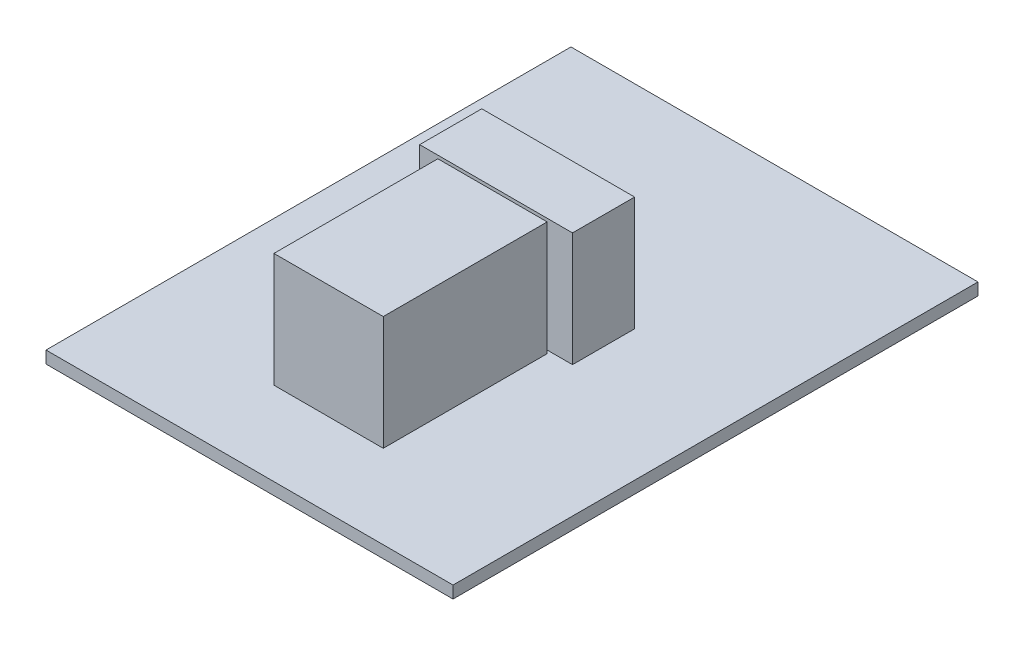
SolidWorks part; units mm, degrees
ref_plane "Front Plane" through (0, 0, 0) normal (0, 0, 1) x (1, 0, 0)
ref_plane "Top Plane" through (0, 0, 0) normal (0, 1, 0) x (1, 0, 0)
ref_plane "Right Plane" through (0, 0, 0) normal (1, 0, 0) x (0, 0, -1)
sketch "Sketch1" plane through (0, 0, 0) normal (0, 1, 0) x (1, 0, 0)
  line L0 (0, 69) -> (0, 0)
  line L1 (0, 0) -> (53.5, 0)
  line L3 (0, 69) -> (53.5, 69)
  line L4 (53.5, 0) -> (53.5, 69)
  dimension "D1" = 53.5
  dimension "D2" = 69
extrude "Boss-Extrude1" add sketch "Sketch1" along normal blind 1.6
sketch "Sketch2" plane through (0, 1.6, 0) normal (0, 1, 0) x (1, 0, 0)
  line L1 (18.9825, 10.9748) -> (33.3533, 10.9748)
  line L2 (18.9825, 10.9748) -> (18.9825, 32.5198)
  line L3 (18.9825, 32.5198) -> (33.3533, 32.5198)
  line L4 (33.3533, 10.9748) -> (33.3533, 32.5198)
  line L5 (16.1779, 32.9338) -> (36.2692, 32.9338)
  line L6 (16.1779, 32.9338) -> (16.1779, 41.0976)
  line L7 (16.1779, 41.0976) -> (36.2692, 41.0976)
  line L8 (36.2692, 32.9338) -> (36.2692, 41.0976)
extrude "Boss-Extrude2" add sketch "Sketch2" along normal blind 15
